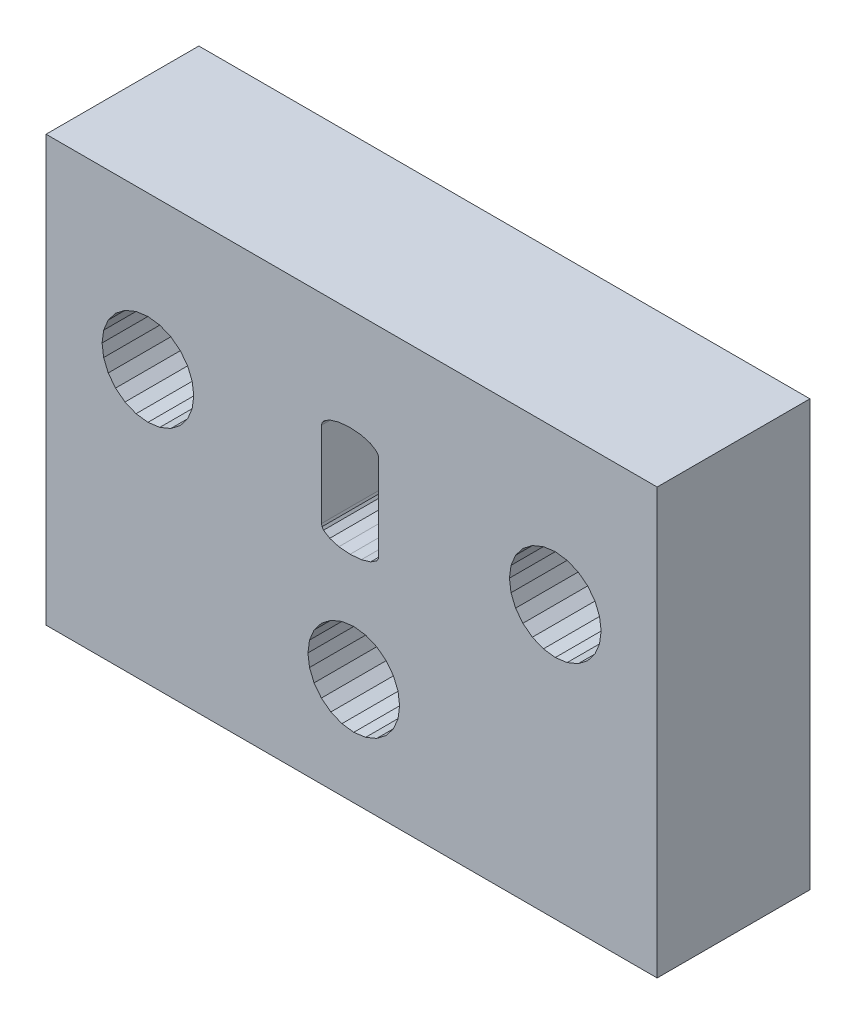
SolidWorks part; units mm, degrees
material "Maple"
ref_plane "Front Plane" through (0, 0, 0) normal (0, 0, 1) x (1, 0, 0)
ref_plane "Top Plane" through (0, 0, 0) normal (0, 1, 0) x (1, 0, 0)
ref_plane "Right Plane" through (0, 0, 0) normal (1, 0, 0) x (0, 0, -1)
sketch "Sketch1" plane through (0, 0, 0) normal (0, 0, 1) x (1, 0, 0)
  line L7084 (254.4205, 82.4661) -> (254.6003, 82.9003)
  line L7085 (251.3028, 84.2661) -> (251.123, 83.832)
  line L7086 (254.4205, 84.2661) -> (254.1345, 84.6389)
  line L7087 (254.1345, 84.6389) -> (253.7617, 84.925)
  line L7088 (253.7617, 84.925) -> (253.3275, 85.1048)
  line L7089 (251.5889, 82.0934) -> (251.9617, 81.8073)
  line L7090 (254.6617, 83.3661) -> (254.6003, 83.832)
  line L7091 (254.6003, 82.9003) -> (254.6617, 83.3661)
  line L7092 (251.5889, 84.6389) -> (251.3028, 84.2661)
  line L7093 (260.3099, 88.1275) -> (260.7758, 88.0661)
  line L7094 (240.7769, 95.8661) -> (264.7769, 95.8661)
  line L7095 (240.7769, 79.1661) -> (240.7769, 95.8661)
  line L7096 (264.7769, 95.8661) -> (264.7769, 79.1661)
  line L7097 (246.3357, 90.7661) -> (246.0497, 91.1389)
  line L7098 (246.0497, 91.1389) -> (245.6769, 91.425)
  line L7099 (262.3346, 88.9661) -> (262.5144, 89.4003)
  line L7100 (260.7758, 88.0661) -> (261.2417, 88.1275)
  line L7101 (262.5144, 90.332) -> (262.3346, 90.7661)
  line L7102 (262.5144, 89.4003) -> (262.5758, 89.8661)
  line L7103 (243.2181, 88.9661) -> (243.5041, 88.5933)
  line L7104 (245.2428, 88.1275) -> (245.6769, 88.3073)
  line L7105 (246.5156, 90.332) -> (246.3357, 90.7661)
  line L7106 (243.0382, 90.332) -> (242.9769, 89.8661)
  line L7107 (264.7769, 79.1661) -> (240.7769, 79.1661)
  line L7108 (262.0486, 88.5933) -> (262.3346, 88.9661)
  line L7109 (242.9769, 89.8661) -> (243.0382, 89.4003)
  line L7110 (258.9758, 89.8661) -> (259.0371, 89.4003)
  line L7111 (260.7758, 91.6661) -> (260.3099, 91.6048)
  line L7112 (252.3958, 85.1048) -> (251.9617, 84.925)
  line L7113 (259.0371, 89.4003) -> (259.2169, 88.9661)
  line L7114 (261.2417, 88.1275) -> (261.6758, 88.3073)
  line L7115 (259.2169, 90.7661) -> (259.0371, 90.332)
  line L7116 (243.2181, 90.7661) -> (243.0382, 90.332)
  line L7117 (262.5758, 89.8661) -> (262.5144, 90.332)
  line L7118 (251.3028, 82.4661) -> (251.5889, 82.0934)
  line L7119 (251.9617, 81.8073) -> (252.3958, 81.6275)
  line L7120 (259.8758, 88.3073) -> (260.3099, 88.1275)
  line L7121 (246.3357, 88.9661) -> (246.5156, 89.4003)
  line L7122 (246.5156, 89.4003) -> (246.5769, 89.8661)
  line L7123 (244.311, 91.6048) -> (243.8769, 91.425)
  line L7124 (253.7617, 81.8073) -> (254.1345, 82.0934)
  line L7125 (254.1345, 82.0934) -> (254.4205, 82.4661)
  line L7126 (254.6003, 83.832) -> (254.4205, 84.2661)
  line L7127 (243.5041, 88.5933) -> (243.8769, 88.3073)
  line L7128 (244.311, 88.1275) -> (244.7769, 88.0661)
  line L7129 (243.8769, 88.3073) -> (244.311, 88.1275)
  line L7130 (262.0486, 91.1389) -> (261.6758, 91.425)
  line L7131 (245.6769, 88.3073) -> (246.0497, 88.5933)
  line L7132 (243.0382, 89.4003) -> (243.2181, 88.9661)
  line L7133 (259.503, 88.5933) -> (259.8758, 88.3073)
  line L7134 (245.6769, 91.425) -> (245.2428, 91.6048)
  line L7135 (246.0497, 88.5933) -> (246.3357, 88.9661)
  line L7136 (251.123, 82.9003) -> (251.3028, 82.4661)
  line L7137 (253.3275, 81.6275) -> (253.7617, 81.8073)
  line L7138 (246.5769, 89.8661) -> (246.5156, 90.332)
  line L7139 (244.7769, 91.6661) -> (244.311, 91.6048)
  line L7140 (245.2428, 91.6048) -> (244.7769, 91.6661)
  line L7141 (261.6758, 88.3073) -> (262.0486, 88.5933)
  line L7142 (251.123, 83.832) -> (251.0617, 83.3661)
  line L7143 (243.5041, 91.1389) -> (243.2181, 90.7661)
  line L7144 (244.7769, 88.0661) -> (245.2428, 88.1275)
  line L7145 (260.3099, 91.6048) -> (259.8758, 91.425)
  line L7146 (243.8769, 91.425) -> (243.5041, 91.1389)
  line L7147 (259.2169, 88.9661) -> (259.503, 88.5933)
  line L7148 (252.3958, 81.6275) -> (252.8617, 81.5661)
  line L7149 (252.8617, 81.5661) -> (253.3275, 81.6275)
  line L7150 (251.0617, 83.3661) -> (251.123, 82.9003)
  line L7151 (252.8617, 85.1661) -> (252.3958, 85.1048)
  line L7152 (262.3346, 90.7661) -> (262.0486, 91.1389)
  line L7153 (261.2417, 91.6048) -> (260.7758, 91.6661)
  line L7154 (261.6758, 91.425) -> (261.2417, 91.6048)
  line L7155 (259.0371, 90.332) -> (258.9758, 89.8661)
  line L7156 (259.503, 91.1389) -> (259.2169, 90.7661)
  line L7157 (253.3275, 85.1048) -> (252.8617, 85.1661)
  line L7158 (251.9617, 84.925) -> (251.5889, 84.6389)
  line L7159 (259.8758, 91.425) -> (259.503, 91.1389)
  line L9522 (251.5942, 88.0309) -> (251.6143, 87.9348)
  line L9523 (251.6143, 87.9348) -> (251.6746, 87.846)
  line L9524 (251.6746, 87.846) -> (251.9158, 87.6907)
  line L9525 (251.9158, 87.6907) -> (252.2771, 87.5853)
  line L9526 (252.2771, 87.5853) -> (252.7181, 87.5502)
  line L9527 (252.7181, 87.5502) -> (253.1591, 87.5853)
  line L9528 (253.1591, 87.5853) -> (253.5205, 87.6907)
  line L9529 (253.5205, 87.6907) -> (253.7616, 87.846)
  line L9530 (253.7616, 87.846) -> (253.8219, 87.9348)
  line L9531 (253.8219, 87.9348) -> (253.842, 88.0309)
  line L9532 (253.842, 88.0309) -> (253.842, 91.3774)
  line L9533 (253.842, 91.3774) -> (253.8219, 91.4735)
  line L9534 (253.8219, 91.4735) -> (253.7616, 91.5623)
  line L9535 (253.7616, 91.5623) -> (253.5205, 91.7176)
  line L9536 (253.5205, 91.7176) -> (253.1591, 91.823)
  line L9537 (253.1591, 91.823) -> (252.7181, 91.8581)
  line L9538 (252.7181, 91.8581) -> (252.2771, 91.823)
  line L9539 (252.2771, 91.823) -> (251.9158, 91.7176)
  line L9540 (251.9158, 91.7176) -> (251.6746, 91.5623)
  line L9541 (251.6746, 91.5623) -> (251.6143, 91.4735)
  line L9542 (251.6143, 91.4735) -> (251.5942, 91.3774)
  line L9543 (251.5942, 91.3774) -> (251.5942, 88.0309)
  line L9544 (253.842, 88.0309) -> (253.8219, 87.9348)
  line L9545 (253.8219, 87.9348) -> (253.7616, 87.846)
  line L9546 (253.7616, 87.846) -> (253.5205, 87.6907)
  line L9547 (253.5205, 87.6907) -> (253.1591, 87.5853)
  line L9548 (253.1591, 87.5853) -> (252.7181, 87.5502)
  line L9549 (252.7181, 87.5502) -> (252.2771, 87.5853)
  line L9550 (252.2771, 87.5853) -> (251.9158, 87.6907)
  line L9551 (251.9158, 87.6907) -> (251.6746, 87.846)
  line L9552 (251.6746, 87.846) -> (251.6143, 87.9348)
  line L9553 (251.6143, 87.9348) -> (251.5942, 88.0309)
  line L9554 (251.5942, 88.0309) -> (251.5942, 91.3774)
  line L9555 (251.5942, 91.3774) -> (251.6143, 91.4735)
  line L9556 (251.6143, 91.4735) -> (251.6746, 91.5623)
  line L9557 (251.6746, 91.5623) -> (251.9158, 91.7176)
  line L9558 (251.9158, 91.7176) -> (252.2771, 91.823)
  line L9559 (252.2771, 91.823) -> (252.7181, 91.8581)
  line L9560 (252.7181, 91.8581) -> (253.1591, 91.823)
  line L9561 (253.1591, 91.823) -> (253.5205, 91.7176)
  line L9562 (253.5205, 91.7176) -> (253.7616, 91.5623)
  line L9563 (253.7616, 91.5623) -> (253.8219, 91.4735)
  line L9564 (253.8219, 91.4735) -> (253.842, 91.3774)
  line L9565 (253.842, 91.3774) -> (253.842, 88.0309)
extrude "Boss-Extrude1" add sketch "Sketch1" along normal blind 6 contours L7107 L7096 L7094 L7095 L9543 L9542 L9541 L9540 L9539 L9538 L9537 L9536 L9535 L9534 L9533 L9532 L9531 L9530 L9529 L9528 L9527 L9526 L9525 L9524 L9523 L9522 L7159 L7145 L7111 L7153 L7154 L7130 L7152 L7101 L7117 L7102 L7099 L7108 L7141 L7114 L7100 L7093 L7120 L7133 L7147 L7113 L7110 L7155 L7115
